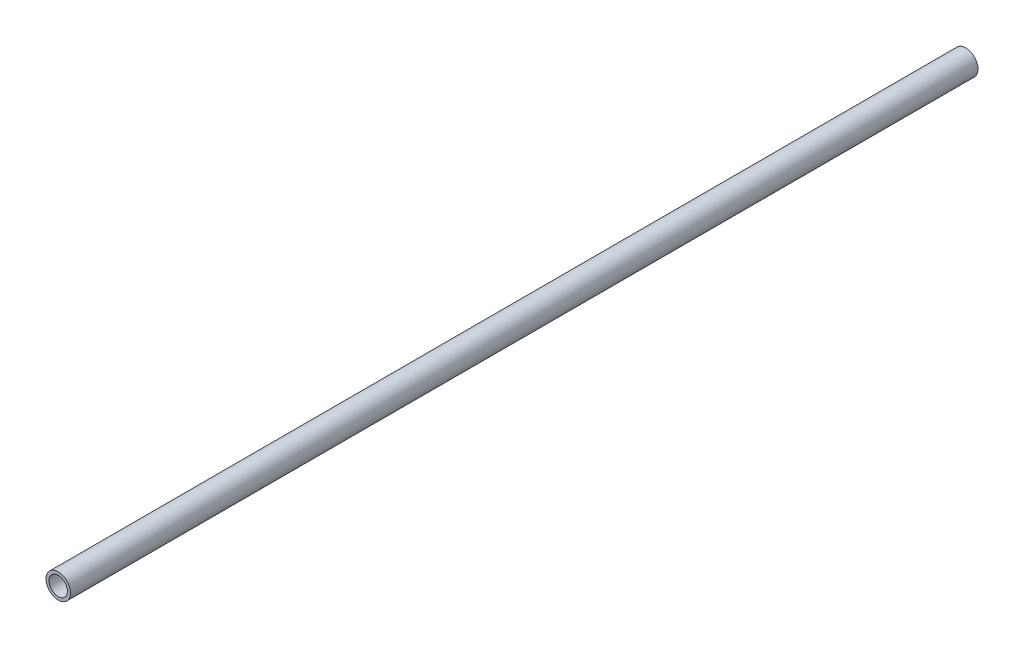
SolidWorks part; units mm, degrees
ref_plane "Front Plane" through (0, 0, 0) normal (0, 0, 1) x (1, 0, 0)
ref_plane "Top Plane" through (0, 0, 0) normal (0, 1, 0) x (1, 0, 0)
ref_plane "Right Plane" through (0, 0, 0) normal (1, 0, 0) x (0, 0, -1)
sketch "Sketch1" plane through (0, 0, 0) normal (0, 0, 1) x (1, 0, 0)
  circle A0 centre (0, 0) radius 12.7
  circle A1 centre (0, 0) radius 9.525
  dimension "D1" = 25.4
  dimension "D2" = 19.05
extrude "Boss-Extrude1" add sketch "Sketch1" along normal blind 939.8
